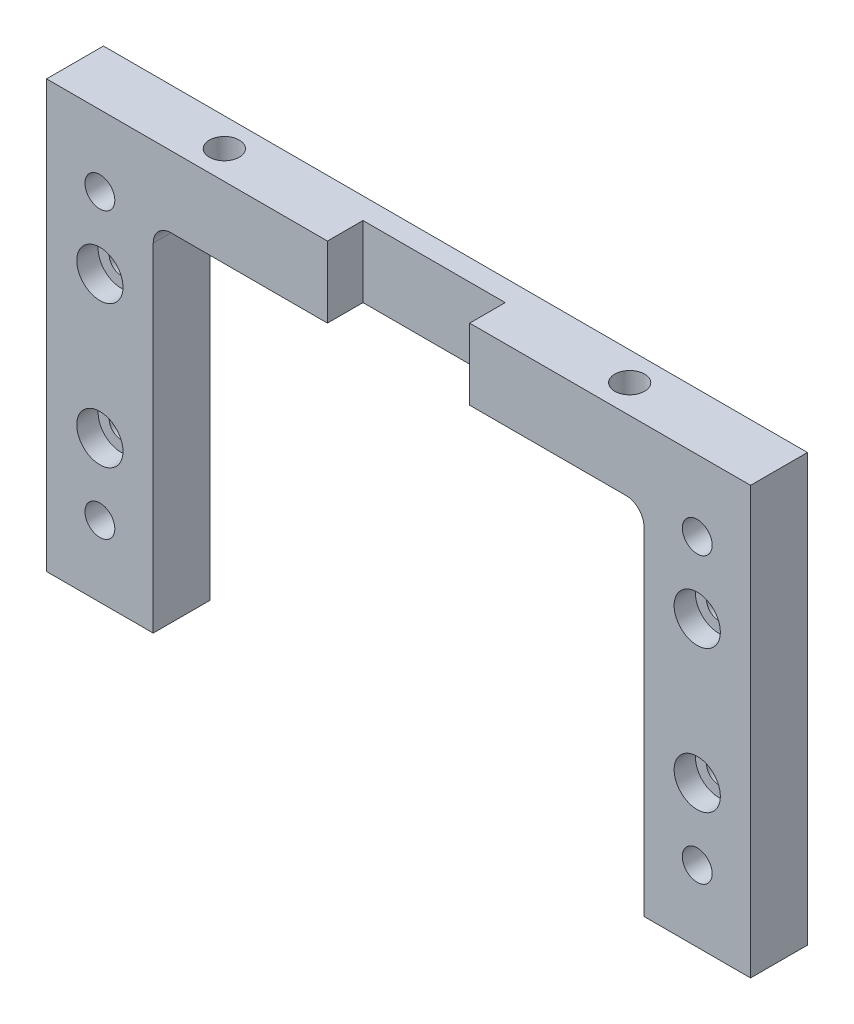
SolidWorks part; units mm, degrees
ref_plane "Front Plane" through (0, 0, 0) normal (0, 0, 1) x (1, 0, 0)
ref_plane "Top Plane" through (0, 0, 0) normal (0, 1, 0) x (1, 0, 0)
ref_plane "Right Plane" through (0, 0, 0) normal (1, 0, 0) x (0, 0, -1)
sketch "Sketch1" plane through (0, 0, 0) normal (0, 0, 1) x (1, 0, 0)
  line L0 (-34.5, 0) -> (-49.5, 0)
  line L1 (-49.5, 0) -> (-49.5, 60)
  line L2 (-49.5, 60) -> (49.5, 60)
  line L3 (49.5, 60) -> (49.5, 0)
  line L4 (49.5, 0) -> (34.5, 0)
  line L5 (34.5, 0) -> (34.5, 47.5)
  line L6 (32, 50) -> (-32, 50)
  line L7 (-34.5, 47.5) -> (-34.5, 0)
  arc A0 (34.5, 47.5) -> (32, 50) centre (32, 47.5) ccw
  arc A1 (-32, 50) -> (-34.5, 47.5) centre (-32, 47.5) ccw
  point P13 (0, 60)
  point P14 (-32, 46.4865)
  dimension "D2" = 2.5
  dimension "D1" = 60
  dimension "D3" = 15
  dimension "D4" = 99
  dimension "D5" = 47.5
extrude "Boss-Extrude1" add sketch "Sketch1" along normal mid plane 8
hole_wizard "CBORE for M3 SHCS2" positions "Sketch2" profile "Sketch3" counterbore size "M3" standard "ANSI Metric" end condition through all
sketch "Sketch2" plane through (0, 0, 4) normal (0, 0, 1) x (1, 0, 0)
  line L0 (-42, 0) -> (-42, 68.2572) construction
  line L1 (-49.5, 0) -> (-34.5, 0) construction
  line L3 (-49.5, 60) -> (-49.5, 0) construction
  point P0 (-42, 40)
  point P2 (-42, 20)
  point P13 (0, 0)
  point P14 (0, 0)
  dimension "D1" = 7.5
  dimension "D2" = 20
  dimension "D3" = 20
sketch "Sketch3" plane through (-42, 40, 4) normal (1, 0, 0) x (0, -1, 0)
  line L0 (0, 0) -> (0, 8)
  line L1 (0, 8) -> (1.7, 8)
  line L3 (1.7, 8) -> (1.7, 3)
  line L4 (1.7, 3) -> (3.25, 3)
  line L5 (3.25, 3) -> (3.25, 0)
  line L7 (3.25, 0) -> (0, 0)
  line L11 (0, -6.35) -> (0, 107.95) construction
  dimension "Thru Hole Dia." = 3.4
  dimension "Thru Hole Depth" = 8
  dimension "C'Bore Dia." = 6.5
  dimension "C'Bore Depth" = 3
hole_wizard "M5x0.8 Tapped Hole1" positions "Sketch4" profile "Sketch5" tap size "M5x0.8" standard "ANSI Metric" end condition through all
sketch "Sketch4" plane through (0, 0, 4) normal (0, 0, 1) x (1, 0, 0)
  line L0 (-42, 0) -> (-42, 67.9436) construction
  line L1 (-49.5, 0) -> (-34.5, 0) construction
  point P0 (-42, 10)
  point P2 (-42, 50)
  dimension "D1" = 10
  dimension "D2" = 40
sketch "Sketch5" plane through (-42, 10, 4) normal (1, 0, 0) x (0, -1, 0)
  line L0 (0, 0) -> (0, 8)
  line L1 (0, 8) -> (2.1, 8)
  line L2 (2.1, 8) -> (2.1, 0)
  line L5 (2.1, 0) -> (0, 0)
  line L11 (0, -6.35) -> (0, 107.95) construction
  dimension "Thru Tap Drill Dia." = 4.2
  dimension "Thru Tap Drill Depth" = 8
cosmetic thread "Hole Thread1" parameters "D2"=5
cosmetic thread "Hole Thread2" parameters "D2"=5
hole_wizard "M5x0.8 Tapped Hole2" positions "Sketch6" profile "Sketch7" tap size "M5x0.8" standard "ANSI Metric" end condition through all
sketch "Sketch6" plane through (0, 60, 0) normal (0, 1, 0) x (1, 0, 0)
  line L0 (-49.5, -4) -> (-49.5, 4) construction
  point P0 (-28.5, 0)
  point P5 (0, 0)
  dimension "D1" = 21
sketch "Sketch7" plane through (-28.5, 60, 0) normal (1, 0, 0) x (0, 0, 1)
  line L0 (0, 0) -> (0, 60)
  line L1 (0, 60) -> (2.1, 60)
  line L2 (2.1, 60) -> (2.1, 0)
  line L5 (2.1, 0) -> (0, 0)
  line L11 (0, -6.35) -> (0, 107.95) construction
  dimension "Thru Tap Drill Dia." = 4.2
  dimension "Thru Tap Drill Depth" = 60
cosmetic thread "Hole Thread3" parameters "D2"=5
mirror "Mirror1" about plane through (0, 0, 0) normal (1, 0, 0) of "M5x0.8 Tapped Hole2", "M5x0.8 Tapped Hole1", "CBORE for M3 SHCS2"
cosmetic thread "Hole Thread4" parameters "D2"=5
cosmetic thread "Hole Thread5" parameters "D2"=5
cosmetic thread "Hole Thread6" parameters "D2"=5
sketch "Sketch8" plane through (0, 0, 4) normal (0, 0, 1) x (1, 0, 0)
  line L0 (-32, 50) -> (32, 50) construction
  line L1 (-10, 50) -> (10, 50)
  line L2 (-10, 50) -> (-10, 60)
  line L3 (-10, 60) -> (10, 60)
  line L4 (10, 50) -> (10, 60)
  line L5 (49.5, 60) -> (-49.5, 60) construction
  line L6 (0, 0) -> (0, 81.2566) construction
  point P13 (0, 60)
  dimension "D1" = 20
extrude "Cut-Extrude1" cut sketch "Sketch8" against normal blind 5
